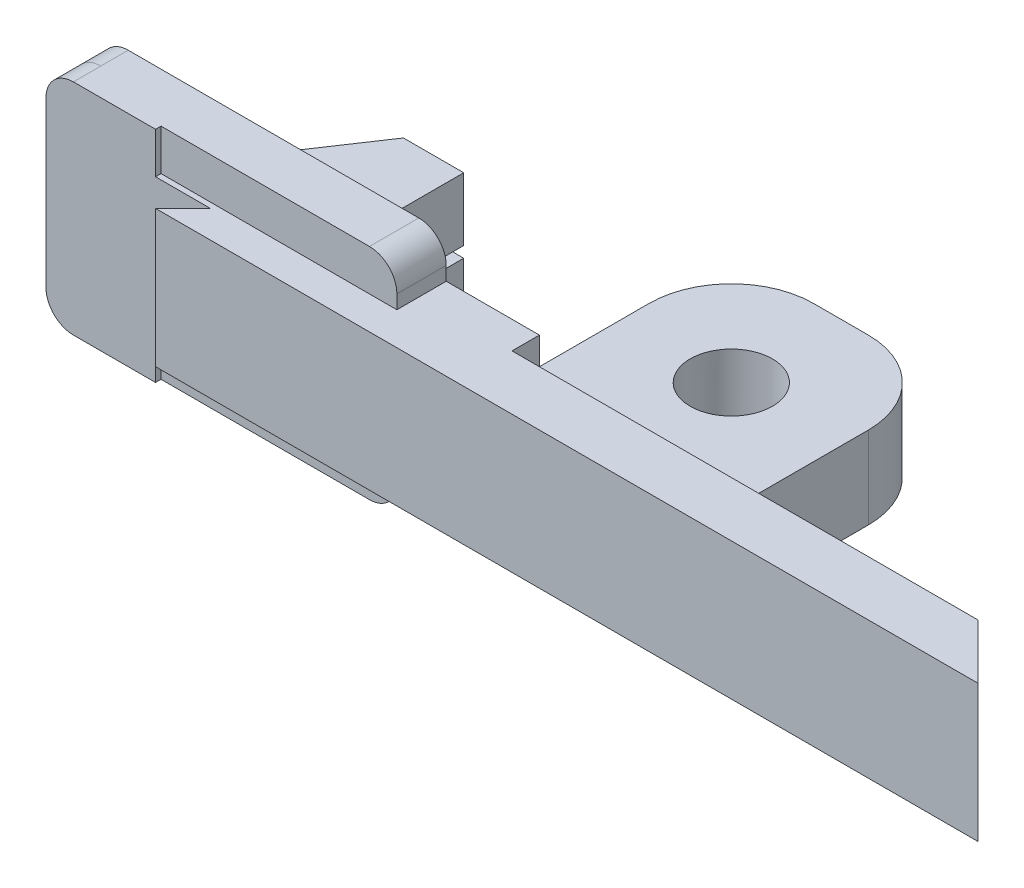
SolidWorks part; units mm, degrees
ref_plane "Płaszczyzna przednia" through (0, 0, 0) normal (0, 0, 1) x (1, 0, 0)
ref_plane "Płaszczyzna górna" through (0, 0, 0) normal (0, 1, 0) x (1, 0, 0)
ref_plane "Płaszczyzna prawa" through (0, 0, 0) normal (1, 0, 0) x (0, 0, -1)
sketch "Szkic1" plane through (0, 0, 0) normal (0, 0, 1) x (1, 0, 0)
  line L1 (-75, -12.5) -> (75, -12.5)
  line L2 (-75, -12.5) -> (-75, 12.5)
  line L3 (-75, 12.5) -> (75, 12.5)
  line L4 (75, -12.5) -> (75, 12.5)
  line L5 (-75, -12.5) -> (75, 12.5) construction
  line L6 (-75, 12.5) -> (75, -12.5) construction
  point P0 (0, 0)
  dimension "D1" = 25
  dimension "D2" = 150
extrude "Dodanie-wyciągnięcie1" add sketch "Szkic1" along normal blind 5
sketch "Szkic2" plane through (0, 12.5, 0) normal (0, 1, 0) x (1, 0, 0)
  line L0 (75, -5) -> (70, 0)
  line L1 (75, -5) -> (-75, -5) construction
  line L2 (75, -5) -> (75, 0) construction
  line L3 (75, 0) -> (-75, 0) construction
  line L4 (70, 0) -> (75, 0)
  line L5 (75, 0) -> (75, -5)
  line L6 (0, -2.75) -> (0, 2.75) construction
  line L7 (-70, 0) -> (-75, 0)
  line L8 (-75, -5) -> (-70, 0)
  line L9 (-75, 0) -> (-75, -5)
  dimension "D1" = 5
extrude "Wytnij-wyciągnięcie1" cut sketch "Szkic2" against normal through all
sketch "Szkic3" plane through (0, 0, 0) normal (0, 0, -1) x (-1, 0, 0)
  line L0 (0, 2.75) -> (0, -2.75) construction
  line L1 (10, -20) -> (100, -20)
  line L2 (10, -20) -> (10, 20)
  line L3 (10, 20) -> (100, 20)
  line L4 (100, -20) -> (100, 20)
  line L5 (10, -20) -> (100, 20) construction
  line L6 (10, 20) -> (100, -20) construction
  point P0 (55, 0)
  dimension "D1" = 10
  dimension "D2" = 100
  dimension "D3" = 40
  dimension "D4" = 20
extrude "Dodanie-wyciągnięcie2" add sketch "Szkic3" along normal blind 5
fillet "Zaokrąglenie1" radius 5 4 edges at (-100, 20, -2.5) (-100, -20, -2.5) (-10, -20, -2.5) (-10, 20, -2.5)
sketch "Szkic4" plane through (0, 0, 0) normal (0, 0, -1) x (-1, 0, 0)
  line L0 (-70, 12.5) -> (10, 12.5) construction
  line L1 (-65, -12.5) -> (10, -12.5)
  line L2 (-65, -12.5) -> (-65, 12.5)
  line L3 (-65, 12.5) -> (10, 12.5)
  line L4 (10, -12.5) -> (10, 12.5)
  line L5 (-65, -12.5) -> (10, 12.5) construction
  line L6 (-65, 12.5) -> (10, -12.5) construction
  line L7 (10, 15) -> (10, -15) construction
  line L9 (-70, -12.5) -> (-70, 12.5) construction
  point P0 (-27.5, 0)
  point P7 (10, 0)
  dimension "D1" = 0
  dimension "D2" = 5
extrude "Dodanie-wyciągnięcie3" add sketch "Szkic4" along normal blind 5
sketch "Szkic5" plane through (0, -12.5, 0) normal (0, -1, 0) x (1, 0, 0)
  line L0 (65, 0) -> (70, 0)
  line L1 (70, 0) -> (65, -5)
  line L2 (65, -5) -> (65, 0)
extrude "Dodanie-wyciągnięcie4" add sketch "Szkic5" against normal blind 25
sketch "Szkic6" plane through (0, 0, -5) normal (0, 0, -1) x (-1, 0, 0)
  line L0 (10, 12.5) -> (-65, 12.5) construction
  line L1 (20, -12.5) -> (-20, -12.5)
  line L2 (20, -12.5) -> (20, 12.5)
  line L3 (20, 12.5) -> (-20, 12.5)
  line L4 (-20, -12.5) -> (-20, 12.5)
  line L5 (20, -12.5) -> (-20, 12.5) construction
  line L6 (20, 12.5) -> (-20, -12.5) construction
  point P0 (0, 0)
  dimension "D1" = 40
extrude "Dodanie-wyciągnięcie5" add sketch "Szkic6" along normal blind 40
fillet "Zaokrąglenie2" radius 15 2 edges at (-20, 0, -45) (20, 0, -45)
sketch "Szkic7" plane through (0, 12.5, 0) normal (0, 1, 0) x (1, 0, 0)
  line L0 (0, -22) -> (0, 22) construction
  line L1 (-5, 45) -> (5, 45) construction
  circle A0 centre (0, 25) radius 7.5
  dimension "D2" = 15
  dimension "D1" = 20
extrude "Wytnij-wyciągnięcie2" cut sketch "Szkic7" against normal blind 40
sketch "Szkic10" plane through (0, 0, 0) normal (0, 0, 1) x (1, 0, 0)
  line L0 (-10, 12.5) -> (-37, 12.5)
  line L1 (-10, 12.5) -> (-70, 12.5) construction
  line L2 (-37, 12.5) -> (-37, 20)
  line L3 (-95, 20) -> (-15, 20) construction
  line L4 (-37, 20) -> (-10, 20)
  line L5 (-10, 20) -> (-10, 12.5)
  line L6 (27.5, 0) -> (-27.5, 0) construction
  line L7 (-37, -20) -> (-10, -20)
  line L8 (-37, -12.5) -> (-37, -20)
  line L9 (-10, -12.5) -> (-37, -12.5)
  line L10 (-10, -20) -> (-10, -12.5)
  dimension "D1" = 27
extrude "Wytnij-wyciągnięcie5" cut sketch "Szkic10" against normal blind 10
sketch "Szkic11" plane through (0, 0, -5) normal (0, 0, -1) x (-1, 0, 0)
  line L1 (37, 20) -> (100, 20)
  line L2 (100, 20) -> (100, -20)
  line L3 (100, -20) -> (37, -20)
  line L4 (37, -20) -> (37, -12.5)
  line L5 (37, -12.5) -> (20, -12.5)
  line L6 (20, -12.5) -> (20, 12.5)
  line L7 (20, 12.5) -> (37, 12.5)
  line L8 (37, 12.5) -> (37, 20)
extrude "Dodanie-wyciągnięcie7" add sketch "Szkic11" along normal blind 5
fillet "Zaokrąglenie5" radius 5 2 edges at (-100, 20, -7.5) (-100, -20, -7.5)
fillet "Zaokrąglenie6" radius 5 2 edges at (-37, 20, -5) (-37, -20, -5)
sketch "Szkic19" plane through (0, 0, 0) normal (0, 1, 0) x (1, 0, 0)
  line L0 (-76.0736, 10) -> (-63.5389, 28.7415)
  line L1 (-95, 10) -> (-42, 10) construction
  line L2 (-63.5389, 28.7415) -> (-52.5463, 28.7415)
  line L3 (-52.5463, 28.7415) -> (-52.5463, 10)
  line L4 (-52.5463, 10) -> (-76.0736, 10)
extrude "Dodanie-wyciągnięcie8" add sketch "Szkic19" along normal mid plane 25
sketch "Szkic21" plane through (-52.5463, 0, 0) normal (1, 0, 0) x (0, 0, -1)
  line L0 (27.5, 0) -> (-27.5, 0) construction
  line L1 (12.9434, 1) -> (28.7415, 1)
  line L2 (12.9434, 1) -> (12.9434, -1)
  line L3 (12.9434, -1) -> (28.7415, -1)
  line L4 (28.7415, 1) -> (28.7415, -1)
  line L5 (12.9434, 1) -> (28.7415, -1) construction
  line L6 (12.9434, -1) -> (28.7415, 1) construction
  line L7 (28.7415, 12.5) -> (28.7415, -12.5) construction
  point P0 (20.8425, 0)
  dimension "D1" = 0
  dimension "D2" = 2
extrude "Wytnij-wyciągnięcie8" cut sketch "Szkic21" against normal blind 25
sketch "Szkic22" plane through (0, 0, 0) normal (0, 1, 0) x (1, 0, 0)
  line L0 (-52.5463, 12) -> (-53.5463, 12)
  line L1 (-52.5463, 10) -> (-52.5463, 28.7415) construction
  line L2 (-52.5463, 20) -> (-53.5463, 20)
  line L3 (-95, 10) -> (-42, 10) construction
  line L4 (-52.5463, 20) -> (-52.5463, 12)
  arc A0 (-53.5463, 20) -> (-53.5463, 12) centre (-53.5463, 16) ccw
  dimension "D1" = 2
  dimension "D2" = 8
  dimension "D3" = 1
  dimension "D4" = 1
  dimension "D5" = 1
extrude "Wytnij-wyciągnięcie9" cut sketch "Szkic22" against normal mid plane 15
sketch "Szkic23" plane through (0, 0, -45) normal (0, 0, -1) x (-1, 0, 0)
  line L0 (-20, 12.5) -> (20, 12.5)
  line L1 (20, 12.5) -> (20, 7.5)
  line L2 (20, 12.5) -> (20, -12.5) construction
  line L3 (20, 7.5) -> (-20, 7.5)
  line L4 (-20, 12.5) -> (-20, -12.5) construction
  line L5 (-20, 7.5) -> (-20, 12.5)
  line L6 (27.5, 0) -> (-27.5, 0) construction
  line L7 (20, -7.5) -> (-20, -7.5)
  line L8 (20, -12.5) -> (20, -7.5)
  line L9 (-20, -12.5) -> (20, -12.5)
  line L10 (-20, -7.5) -> (-20, -12.5)
  dimension "D1" = 5
extrude "Wytnij-wyciągnięcie10" cut sketch "Szkic23" against normal blind 40
sketch "Szkic24" plane through (0, 0, 0) normal (0, 0, 1) x (1, 0, 0)
  line L0 (-75, 12.5) -> (-37, 12.5)
  line L1 (-37, 12.5) -> (-37, 20)
  line L2 (-37, 20) -> (-75, 20)
  line L3 (-95, 20) -> (-42, 20) construction
  line L4 (-75, 12.5) -> (-75, 20)
  line L5 (-75, -12.5) -> (-75, -20)
  line L6 (-42, -20) -> (-95, -20) construction
  line L7 (-75, -20) -> (-37, -20)
  line L8 (-37, -20) -> (-37, -12.5)
  line L9 (-37, -12.5) -> (-75, -12.5)
  point P13 (-75, -12.5)
extrude "Wytnij-wyciągnięcie11" cut sketch "Szkic24" against normal blind 1
sketch "Szkic25" plane through (0, 0, 0) normal (0, 0, 1) x (1, 0, 0)
  line L0 (-75, 12.5) -> (-80.0167, 12.5)
  line L1 (-80.0167, 12.5) -> (-80.0167, 20)
  line L2 (-95, 20) -> (-75, 20) construction
  line L3 (-80.0167, 20) -> (-75, 20)
  line L4 (-75, 20) -> (-75, 12.5)
  line L5 (27.5, 0) -> (-27.5, 0) construction
  line L6 (-80.0167, -20) -> (-75, -20)
  line L7 (-75, -12.5) -> (-80.0167, -12.5)
  line L8 (-80.0167, -12.5) -> (-80.0167, -20)
  line L9 (-75, -20) -> (-75, -12.5)
extrude "Wytnij-wyciągnięcie12" cut sketch "Szkic25" against normal blind 1
